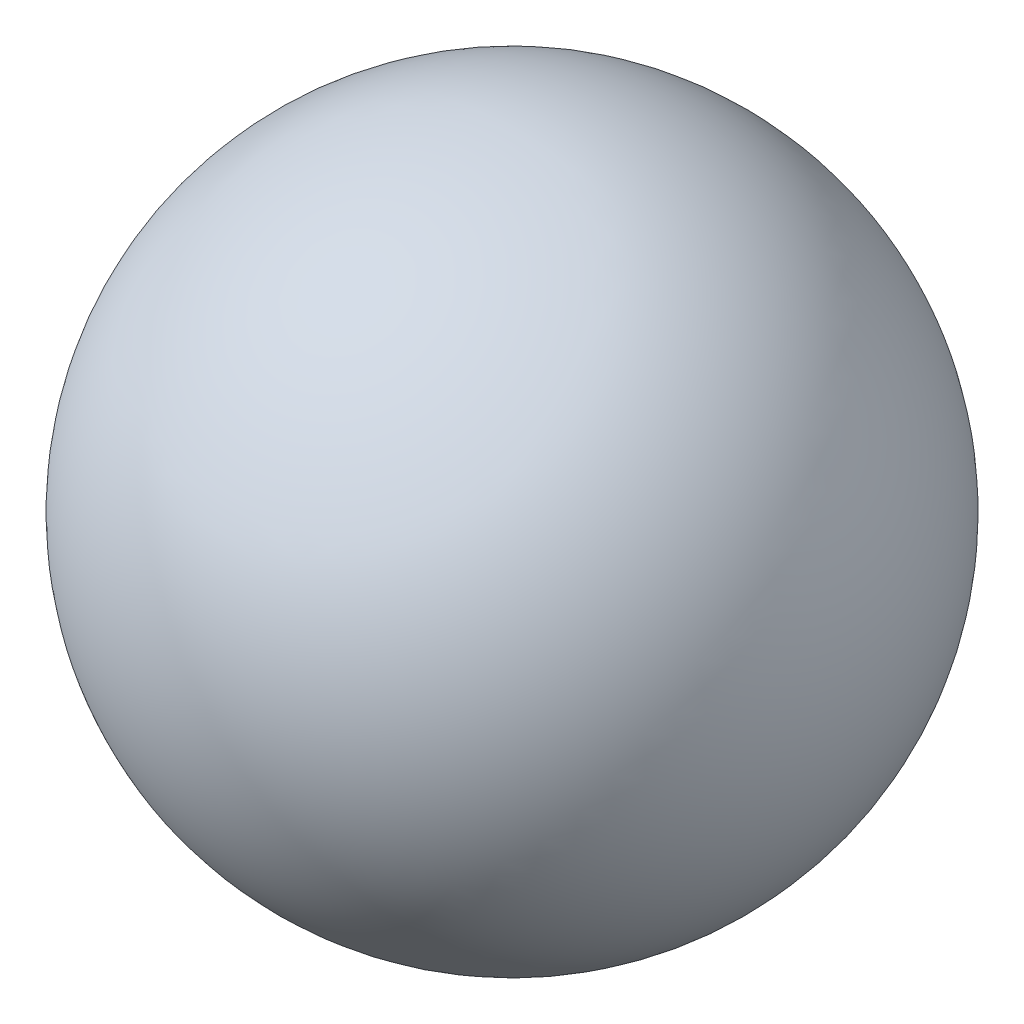
SolidWorks part; units mm, degrees
ref_plane "Front Plane" through (0, 0, 0) normal (0, 0, 1) x (1, 0, 0)
ref_plane "Top Plane" through (0, 0, 0) normal (0, 1, 0) x (1, 0, 0)
ref_plane "Right Plane" through (0, 0, 0) normal (1, 0, 0) x (0, 0, -1)
sketch "Sketch1" plane through (0, 0, 0) normal (0, 1, 0) x (1, 0, 0)
  line L0 (0, -39) -> (0, 39)
  arc A0 (0, 39) -> (0, -39) centre (0, 0) ccw
  dimension "D1" = 39
revolve "Revolve1" add sketch "Sketch1" angle 360 about L0
sketch "Sketch2" plane through (0, 0, 0) normal (0, 0, 1) x (1, 0, 0)
  circle A0 centre (0, 0) radius 10.5
  dimension "D1" = 21
extrude "Cut-Extrude1" cut sketch "Sketch2" against normal blind 151
